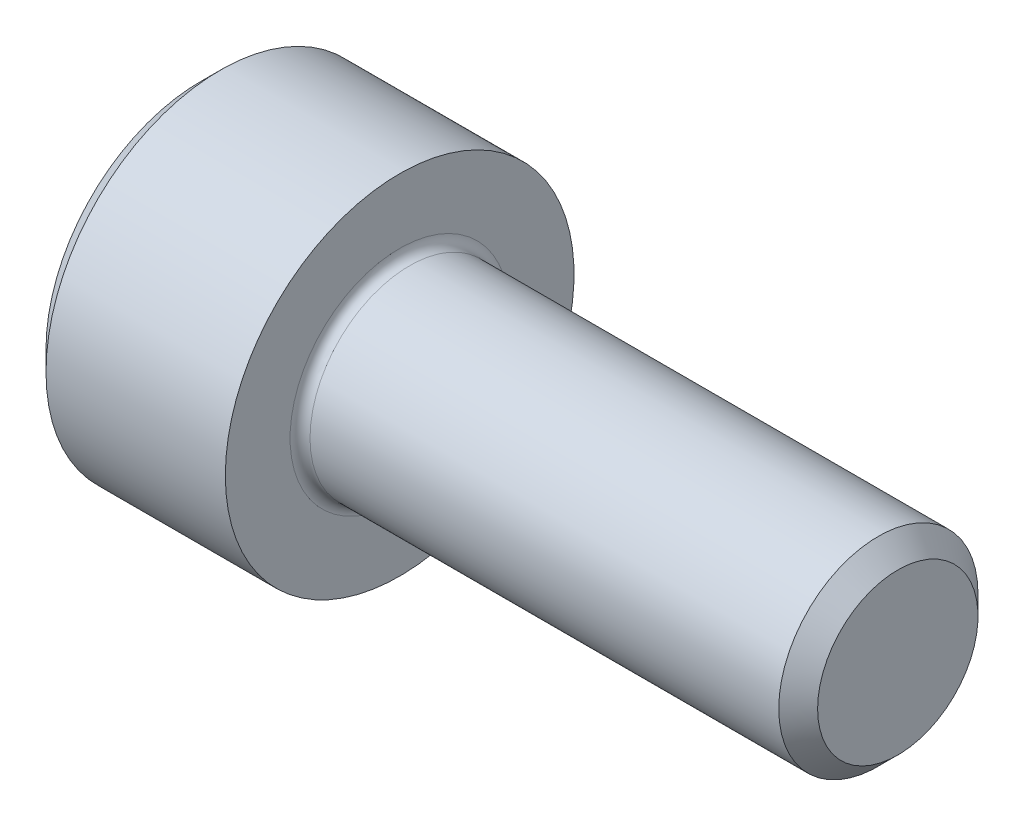
SolidWorks part; units mm, degrees
ref_plane "Plane1" through (0, 0, 0) normal (0, 0, 1) x (1, 0, 0)
ref_plane "Plane2" through (0, 0, 0) normal (0, 1, 0) x (1, 0, 0)
ref_plane "Plane3" through (0, 0, 0) normal (1, 0, 0) x (0, 0, -1)
sketch "BodySke" plane through (0, 0, 0) normal (0, 0, 1) x (1, 0, 0)
  line L0 (0, 0) -> (0, 3.1)
  line L1 (0.4, 3.5) -> (4, 3.5)
  line L2 (4, 3.5) -> (4, 2)
  line L3 (4, 2) -> (13.61, 2)
  line L4 (14, 1.61) -> (14, 0)
  line L5 (14, 0) -> (0, 0)
  line L6 (-31.75, 0) -> (127, 0) construction
  line L7 (0, 3.1) -> (0.4, 3.5)
  line L8 (14, 1.61) -> (13.61, 2)
  line L9 (0, -3.1) -> (0.4, -3.5) construction
  line L10 (14, -1.61) -> (13.61, -2) construction
  line L11 (4.7, 9.525) -> (4.7, 3.175) construction
  line L12 (4, 9.525) -> (4, 3.175) construction
  line L13 (-36, 9.525) -> (-36, 3.175) construction
  dimension "Diameter" = 4
  dimension "Head_ht" = 4
  dimension "Length" = 10
  dimension "Body_ch_ang" = 45
  dimension "Head_dia" = 7
  dimension "Head_ch_ang" = 45
  dimension "Minor_dia" = 3.22
  dimension "Advance" = 0.7
  dimension "Thread_nom" = 10
  dimension "Thread_length" = 50
  dimension "Head_ch_ht" = 0.4
revolve "Base-Revolve" add sketch "BodySke"
cosmetic thread "ThreadCosmetic" [suppressed]
fillet "Fillet1" radius 0.2 1 edges at (4, 0, 2)
sketch "Sketch2" plane through (0, 0, 0) normal (0, 0, 1) x (1, 0, 0)
  line L0 (0, 1.5355) -> (2, 1.5355)
  line L1 (2, 1.5355) -> (2.8865, 0)
  line L2 (-31.75, 0) -> (127, 0) construction
  line L3 (2.8865, 0) -> (0, 0)
  line L4 (0, 0) -> (0, 1.5355)
  line L5 (0, 3.1) -> (0, -3.1) construction
  line L6 (0, 0) -> (47.625, 0) construction
  line L7 (4, -3.5) -> (4, 3.5) construction
  dimension "D1" = 1.5355
  dimension "D2" = 60
  dimension "Wall_thickness" = 2
revolve "Hex-PreBroach" cut sketch "Sketch2" angle 360 about L6
sketch "Sketch3" plane through (0, 0, 0) normal (-1, 0, 0) x (0, 0.5, 0.866)
  line L0 (0.8865, 1.5355) -> (-0.8865, 1.5355)
  line L1 (-0.8865, 1.5355) -> (-1.773, 0)
  line L2 (0.8865, 1.5355) -> (1.773, 0)
  line L3 (0.8865, -1.5355) -> (1.773, 0)
  line L4 (0.8865, -1.5355) -> (-0.8865, -1.5355)
  line L5 (-0.8865, -1.5355) -> (-1.773, 0)
  dimension "D1" = 1.5355
  dimension "D2" = 1.5355
  dimension "Hex_size" = 3.071
extrude "Hex" cut sketch "Sketch3" against normal blind 2
sketch "Sketch4" plane through (0, 0, 0) normal (-1, 0, 0) x (0, 0, 1)
  line L0 (0, 0) -> (1.7399, 0)
  line L1 (0, 0) -> (6.1484, 3.5498) construction
  line L2 (0, 0) -> (0.8699, 1.5068)
  line L3 (1.4457, 0.3947) -> (1.6607, 0.5189)
  line L4 (1.0647, 1.0546) -> (1.2797, 1.1788)
  arc A0 (1.4457, 0.3947) -> (1.0647, 1.0546) centre (0, 0) ccw
  arc A1 (1.7399, 0) -> (1.6607, 0.5189) centre (0, 0) ccw
  arc A2 (0.8699, 1.5068) -> (1.2797, 1.1788) centre (0, 0) cw
  dimension "D1" = 30
  dimension "Spline_n_dim" = 2.9972
  dimension "Spline_m_dim" = 3.4798
  dimension "D2" = 60
  dimension "D3" = 0.381
  dimension "Spline_p_dim" = 0.762
extrude "Spline" [suppressed] cut sketch "Sketch4" against normal blind 2
pattern_circular "CirPattern1" [suppressed] count 6 every 60
sketch "Sketch5" plane through (0, 0, 0) normal (0, 0, 1) x (1, 0, 0)
  line L0 (-31.75, 0) -> (127, 0) construction
  line L2 (0, 3.1) -> (0, -3.1) construction
  circle A0 centre (1.6, 0) radius 0.675
  dimension "Drilled_hole_dia" = 1.35
  dimension "Drilled_hole_loc" = 1.6
extrude "Hole" [suppressed] cut sketch "Sketch5" against normal through all and the other way through all
pattern_circular "Drilled-4" [suppressed] count 2 every 60
pattern_circular "Drilled-6" [suppressed] count 3 every 60
sketch "ThdSchSke" plane through (0, 0, 0) normal (0, 0, 1) x (1, 0, 0)
  line L0 (4.7, -1.61) -> (4.4269, -2)
  line L1 (4.7, -1.61) -> (4.9731, -2)
  line L2 (4.9731, -2) -> (4.9731, -2.5)
  line L3 (-3.175, 0) -> (5.1513, 0) construction
  line L5 (4.9731, -2.5) -> (4.4269, -2.5)
  line L6 (4.4269, -2.5) -> (4.4269, -2)
  line L7 (0, 3.1) -> (0, -3.1) construction
  dimension "Thread_minor" = 3.22
  dimension "Diameter" = 4
  dimension "Start" = 4.7
  dimension "SideAngle" = 55
  dimension "VeeAngle" = 70
  dimension "Overcut" = 5
revolve "ThreadSchematic" [suppressed] cut sketch "ThdSchSke" angle 360 about L3
pattern_linear "ThdSchPat" [suppressed]
equation "\"D2@Sketch3\" = \"Hex_size@Sketch3\" / 2"
equation "\"D1@Sketch3\" = \"Hex_size@Sketch3\" / 2"
equation "\"D1@Sketch2\" = \"Hex_size@Sketch3\" / 2"
equation "\"D3@Sketch4\" = \"Spline_p_dim@Sketch4\" / 2"
equation "\"Thread_minor@ThreadCosmetic\"  =  \"Minor_dia@BodySke\""
equation "\"D2@CirPattern1\" = 360 / \"Num_teeth@CirPattern1\""
equation "\"Wall_thickness@Sketch2\" = \"Head_ht@BodySke\" - \"Key_eng@Hex\""
equation "\"Thread_length@ThreadCosmetic\" = ((sgn( (\"Length@BodySke\" - \"Advance@BodySke\" ) - \"Thread_nom@BodySke\" )-1)*( (\"Length@BodySke\" - \"Advance@BodySke\" ) - \"Thread_nom@BodySke\" ))/-2+ \"Thread_nom@BodySke\""
equation "\"Thread_minor@ThdSchSke\" = \"Minor_dia@BodySke\""
equation "\"Diameter@ThdSchSke\" = \"Diameter@BodySke\""
equation "\"Overcut@ThdSchSke\" = \"Diameter@BodySke\" * 1.25"
equation "\"Start@ThdSchSke\" = \"Head_ht@BodySke\" + \"Length@BodySke\" - \"Thread_length@ThreadCosmetic\"  '---Non-countersunk---"
equation "\"Num_threads@ThdSchPat\" = int( \"Thread_length@ThreadCosmetic\" / \"Advance@BodySke\" + 0.999 )  + 1"
equation "\"Advance@ThdSchPat\" = \"Thread_length@ThreadCosmetic\" /  (\"Num_threads@ThdSchPat\" - 1) 'relax it"
equation "\"Num_threads@ThdSchPat\" = \"Num_threads@ThdSchPat\" - sgn( \"Num_threads@ThdSchPat\" - 1) '---chamfered tips only---"
